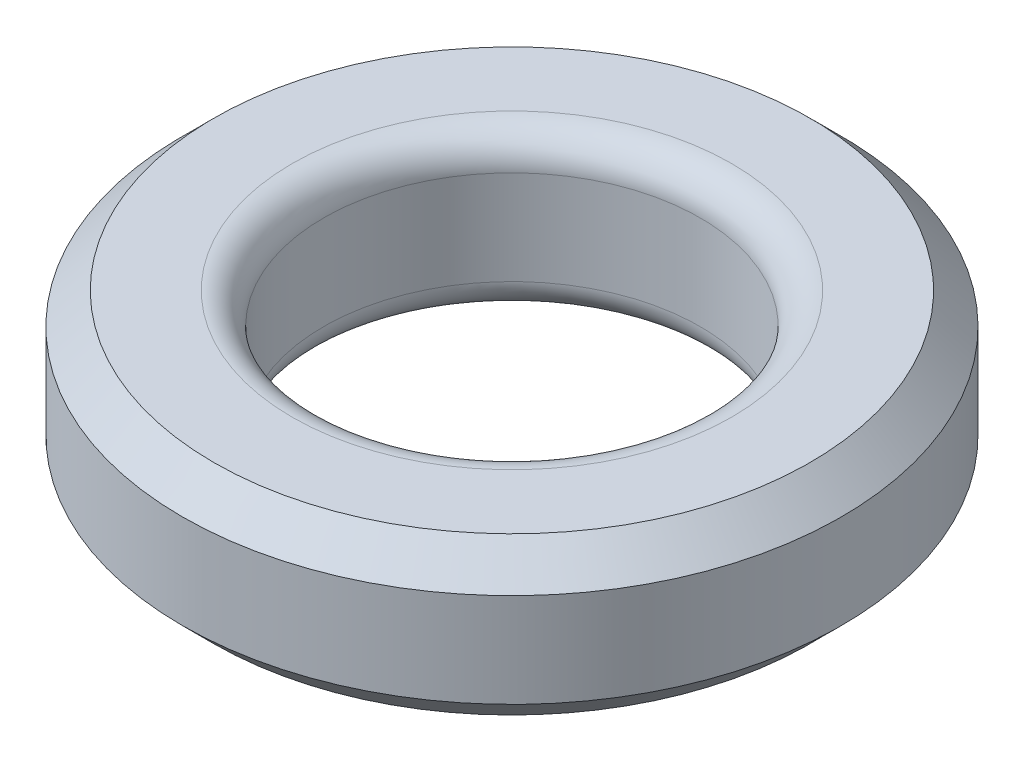
SolidWorks part; units mm, degrees
material "AISI 1020"
ref_plane "Спереди" through (0, 0, 0) normal (0, 0, 1) x (1, 0, 0)
ref_plane "Сверху" through (0, 0, 0) normal (0, 1, 0) x (1, 0, 0)
ref_plane "Справа" through (0, 0, 0) normal (1, 0, 0) x (0, 0, -1)
sketch "Эскиз1" plane through (0, 0, 0) normal (0, 1, 0) x (1, 0, 0)
  circle A0 centre (0, 0) radius 10.5
  circle A1 centre (0, 0) radius 6
  dimension "D1" = 21
  dimension "D2" = 12
extrude "Бобышка-Вытянуть1" add sketch "Эскиз1" along normal blind 5
fillet "Скругление1" radius 1 2 edges at (0, 0, 6) (0, 5, 6)
chamfer "Фаска1" distance 1 angle 45 2 edges at (0, 5, 10.5) (0, 0, 10.5)
